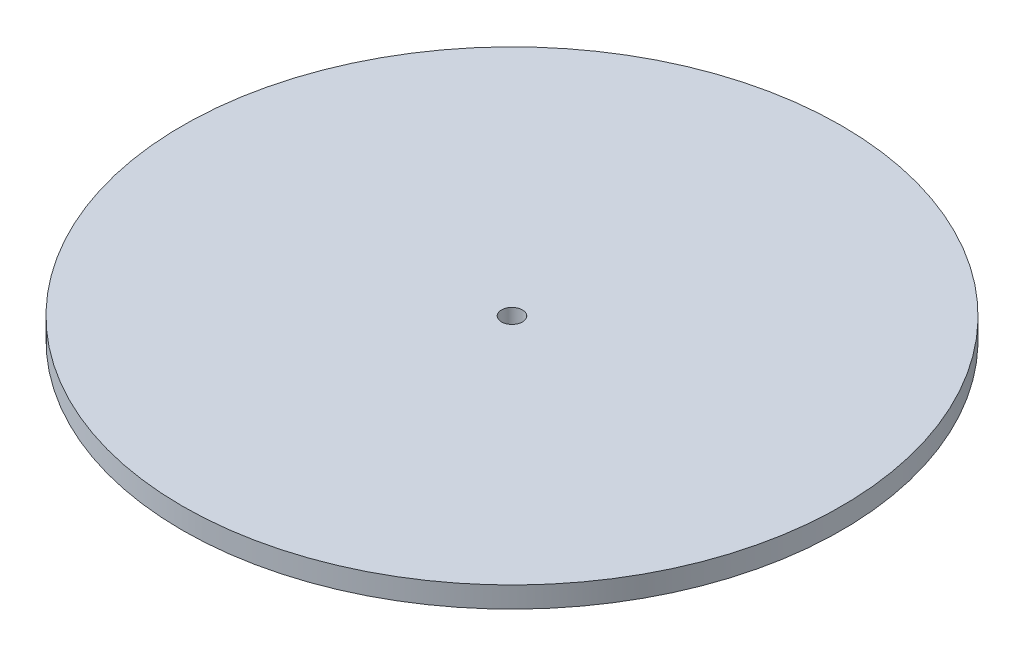
SolidWorks part; units mm, degrees
ref_plane "Front Plane" through (0, 0, 0) normal (0, 0, 1) x (1, 0, 0)
ref_plane "Top Plane" through (0, 0, 0) normal (0, 1, 0) x (1, 0, 0)
ref_plane "Right Plane" through (0, 0, 0) normal (1, 0, 0) x (0, 0, -1)
sketch "Sketch1" plane through (0, 0, 0) normal (0, 1, 0) x (1, 0, 0)
  circle A0 centre (0, 0) radius 400
  circle A1 centre (0, 0) radius 12.7
extrude "Boss-Extrude1" add sketch "Sketch1" along normal blind 25.4
